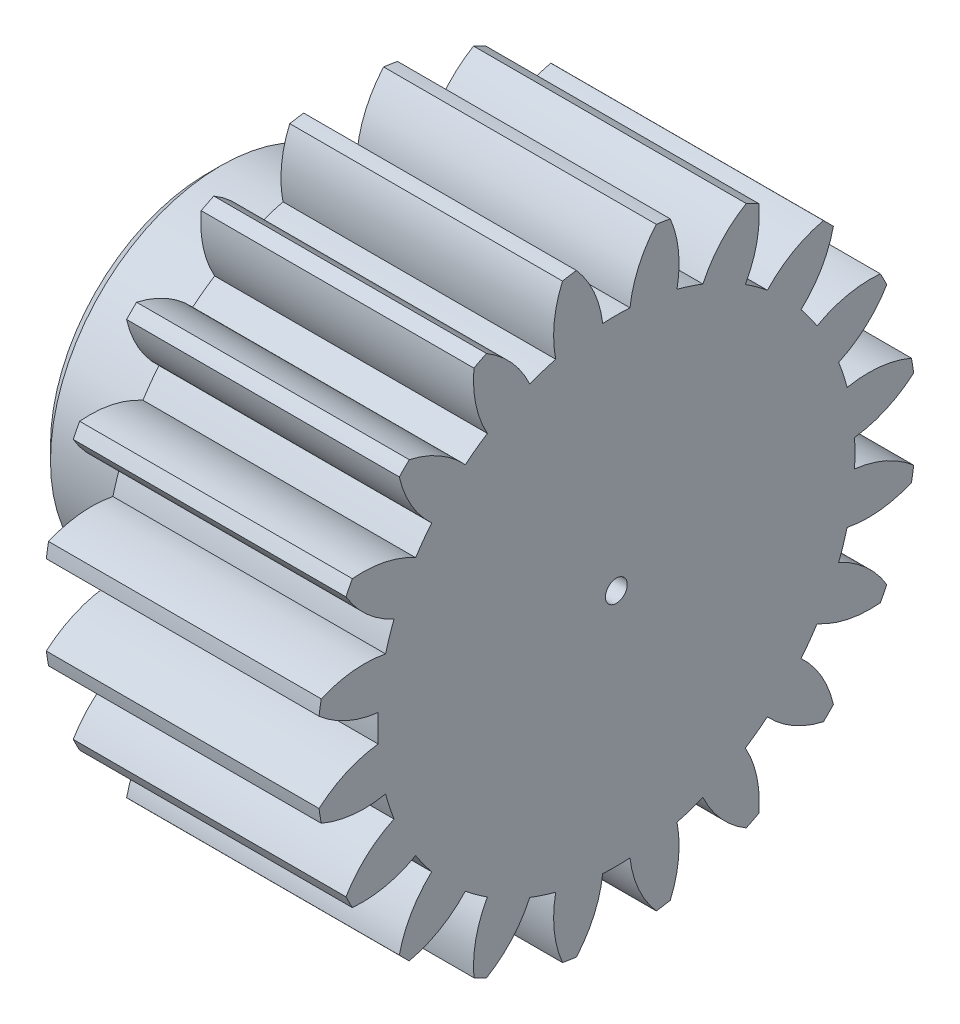
SolidWorks part; units mm, degrees
ref_plane "Front Plane" through (0, 0, 0) normal (0, 0, 1) x (1, 0, 0)
ref_plane "Top Plane" through (0, 0, 0) normal (0, 1, 0) x (1, 0, 0)
ref_plane "Right Plane" through (0, 0, 0) normal (1, 0, 0) x (0, 0, -1)
sketch "HoldingSke" plane through (0, 0, 0) normal (0, 1, 0) x (1, 0, 0)
  line L0 (0, 0) -> (0.9397, -0.342)
  line L1 (-15, 0) -> (100, 0) construction
  line L2 (0, 0) -> (-2.1039, 2.3779)
  line L3 (0, 0) -> (-11.863, 4.5341)
  line L4 (0, 0) -> (8.1152, 2.9537)
  line L5 (0, 0) -> (-46.8476, -17.4728)
  line L6 (0, 0) -> (-8.2896, -5.593)
  line L7 (-2.1039, 2.3779) -> (8.6586, 51.2059)
  line L8 (-76.2, 54.61) -> (-76.1, 54.61)
  line L9 (-71.009, 38.7566) -> (-53.1078, 45.2721)
  line L10 (-76.2, 71.12) -> (104.1128, 71.12)
  line L11 (0, 0) -> (-10, 0)
  line L12 (-76.2, 101.6) -> (-76.162, 101.6)
  line L13 (24.9733, 27.94) -> (52.9518, 28.4284)
  line L14 (24.9733, 27.94) -> (24.9743, 27.94)
  line L15 (24.9733, 27.94) -> (100.4006, 29.5858)
  line L16 (-63.627, -1) -> (-12.827, -1)
  circle A0 centre (0, 0) radius 0.4
  circle A1 centre (0, 0) radius 8.749
  circle A2 centre (0, 0) radius 37.5
  circle A3 centre (0, 0) radius 0.4
  dimension "MHD" = 17.498
  dimension "Hub_dia" = 75
  dimension "Bore" = 0.8
  dimension "MBD" = 0.8
  dimension "Num_teeth" = 20
  dimension "Pitch_radius" = 180.3128
  dimension "Pitch" = 1
  dimension "Width" = 10
  dimension "Overall_len" = 50
  dimension "Show_teeth" = 20
  dimension "Thickness" = 10
  dimension "OAL" = 50.0001
  dimension "T_dim" = 0.1
  dimension "Ap" = 20
  dimension "H" = 19.05
  dimension "Backlash" = 0.038
  dimension "Addendum_fac" = 1
  dimension "Dedendum_fac" = 1.25
  dimension "Clearance_fac" = 0.25
  dimension "Dedendum_add" = 0.001
  dimension "Module" = 1
sketch "BasProSke" plane through (0, 0, 0) normal (0, 1, 0) x (1, 0, 0)
  line L0 (-10, 0) -> (60, 0) construction
  line L1 (0, 0) -> (0, 11)
  line L2 (0, 0) -> (10, 0)
  line L3 (10, 0) -> (10, 11)
  line L4 (10, 11) -> (0, 11)
  dimension "Diameter" = 22
  dimension "Thickness" = 10
revolve "Base-Revolve" add sketch "BasProSke" angle 360 about L0
sketch "TooCutSke" plane through (0, 0, 0) normal (1, 0, 0) x (0, 0, -1)
  line L1 (0, 0) -> (0, 107) construction
  line L2 (0, 0) -> (-0.8511, 9.9637) construction
  line L3 (0, 0) -> (-3.1206, 19.7028) construction
  line L4 (-0.8511, 9.9637) -> (-1.5603, 9.8514) construction
  arc A0 (0.4999, 8.7347) -> (-0.4999, 8.7347) centre (0, 0) ccw
  arc A1 (1.4852, 10.9249) -> (-1.4852, 10.9249) centre (0, 0) ccw
  circle A2 centre (0, 0) radius 10 construction
  circle A3 centre (0, 0) radius 9.3969 construction
  arc A4 (-0.4999, 8.7347) -> (-1.4852, 10.9249) centre (-4.4722, 8.2645) ccw
  arc A5 (1.4852, 10.9249) -> (0.4999, 8.7347) centre (4.4722, 8.2645) ccw
  dimension "Root_dia" = 17.498
  dimension "Overcut_dia" = 22.0508
  dimension "Pitch_dia" = 20
  dimension "Base_dia" = 18.7939
  dimension "Flank_rad" = 4
  dimension "Half_ang" = 9
  dimension "Half_CT" = 0.7181
extrude "ToothCut" cut sketch "TooCutSke" along normal through all
fillet "Breaks" [suppressed] radius 0.02
fillet "RootFillets" [suppressed] radius 0.251
pattern_circular "TeethCuts" count 20 every 18 about axis through (-10, 0, 0) along (1, 0, 0) of "ToothCut", "RootFillets", "Breaks"
sketch "HubNeaOneSke" plane through (0, 0, 0) normal (-1, 0, 0) x (0, 0, 1)
  circle A0 centre (0, 0) radius 8.749
  dimension "Diameter" = 17.498
extrude "HubNearOne" [suppressed] add sketch "HubNeaOneSke" along normal blind 40.0001
sketch "HubNeaBotSke" plane through (0, 0, 0) normal (-1, 0, 0) x (0, 0, 1)
  circle A0 centre (0, 0) radius 8.749
  dimension "Diameter" = 17.498
extrude "HubNearBoth" [suppressed] add sketch "HubNeaBotSke" along normal blind 20
ref_plane "FarPln" through (10, 0, 0) normal (1, 0, 0) x (0, 0, -1)
sketch "HubFarSke" plane through (10, 0, 0) normal (1, 0, 0) x (0, 0, -1)
  circle A0 centre (0, 0) radius 8.749
  dimension "Diameter" = 17.498
extrude "HubFar" [suppressed] add sketch "HubFarSke" along normal blind 20
sketch "BorSke" plane through (0, 0, 0) normal (1, 0, 0) x (0, 0, -1)
  circle A0 centre (0, 0) radius 0.4
  dimension "Diameter" = 0.8
extrude "Bore" cut sketch "BorSke" along normal mid plane 100.0001
sketch "KeySke" plane through (0, 0, 0) normal (1, 0, 0) x (0, 0, -1)
  line L0 (-0.05, 0) -> (-0.05, 0.5)
  line L1 (-0.05, 0.5) -> (0.05, 0.5)
  line L2 (0.05, 0.5) -> (0.05, 0)
  line L3 (0, 0) -> (0, 34) construction
  line L4 (-0.05, 0) -> (0.05, 0)
  dimension "Offset" = 0.5
  dimension "Width" = 0.1
extrude "Keyway" [suppressed] cut sketch "KeySke" along normal mid plane 100.0001
pattern_circular "Keyway2" [suppressed] count 2 every 90 about axis through (-10, 0, 0) along (1, 0, 0)
sketch "Sketch1" plane through (0, 0, 0) normal (-1, 0, 0) x (0, 0, 1)
  circle A0 centre (0, 0) radius 6.25
  dimension "D1" = 12.5
extrude "Boss-Extrude1" add sketch "Sketch1" along normal blind 5
sketch "Sketch2" plane through (0, 0, 0) normal (1, 0, 0) x (0, 0, -1)
  line L0 (-2.5, -1.4434) -> (2.5, -1.4434)
  line L1 (2.5, -1.4434) -> (0, 2.8868)
  line L2 (0, 2.8868) -> (-2.5, -1.4434)
  line L3 (0, -1.4434) -> (0, 2.8868) construction
  line L4 (-2.5, -1.4434) -> (1.25, 0.7217) construction
  point P4 (0, 0)
  point P9 (1.25, 0.7217)
  dimension "D1" = 60
  dimension "D2" = 5
fillet "Fillet1" radius 0.5 1 edges at (0, 0, -6.25)
chamfer "Chamfer1" distance 0.5 angle 45 1 edges at (-5, 0, 6.25)
ref_plane "Midplane" through (5, 0, 0) normal (-1, 0, 0) x (0, 0, 1)
sketch "Sketch3" plane through (5, 0, 0) normal (-1, 0, 0) x (0, 0, 1)
  line L0 (0, 0) -> (0, 10)
  circle A0 centre (0, 0) radius 10
  dimension "D1" = 20
sketch "Sketch4" plane through (-5, 0, 0) normal (-1, 0, 0) x (0, 0, 1)
  circle A0 centre (0, 0) radius 2.5
  dimension "D1" = 5
extrude "Cut-Extrude1" cut sketch "Sketch4" against normal blind 2.5
